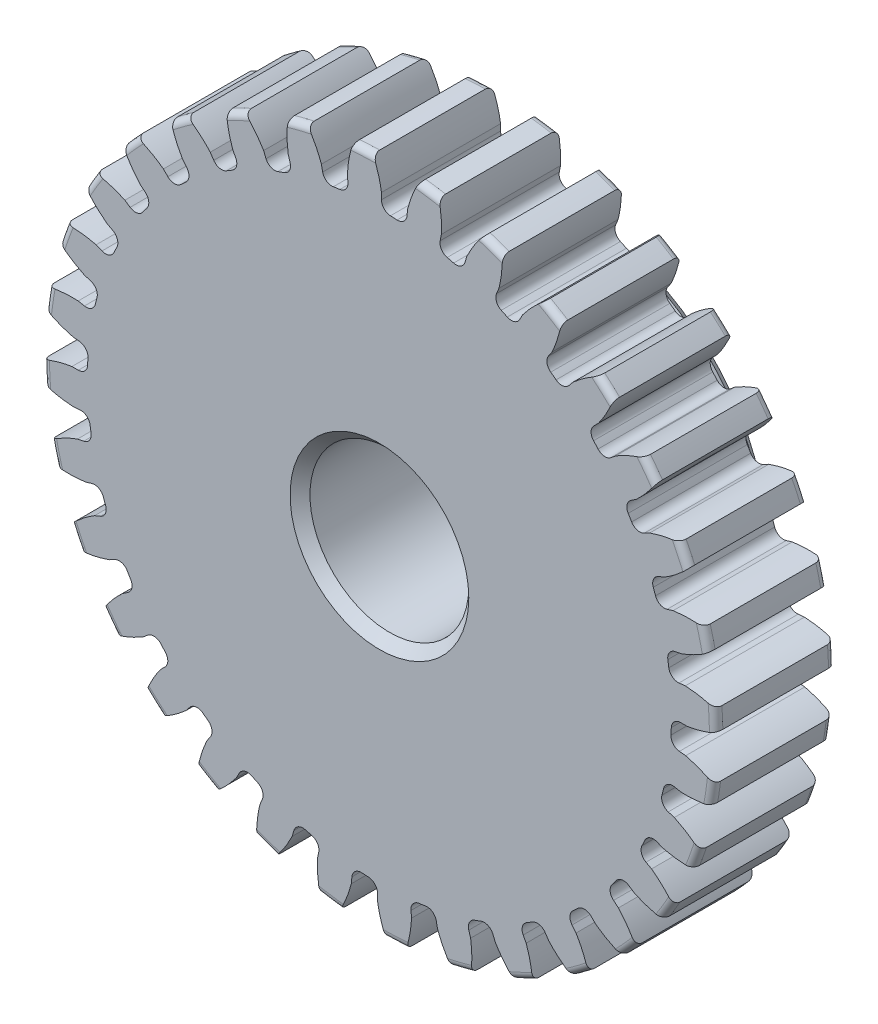
SolidWorks part; units mm, degrees
ref_plane "Front" through (0, 0, 0) normal (0, 0, 1) x (1, 0, 0)
ref_plane "Top" through (0, 0, 0) normal (0, 1, 0) x (1, 0, 0)
ref_plane "Right" through (0, 0, 0) normal (1, 0, 0) x (0, 0, -1)
sketch "Sketch1" plane through (0, 0, 0) normal (0, 0, 1) x (1, 0, 0)
  line L0 (-406.4, 0) -> (406.4, 0) construction
  circle A0 centre (0, 0) radius 13.462
  circle A1 centre (0, 0) radius 12.7 construction
  circle A3 centre (0, 0) radius 11.6761 construction
  dimension "D1" = 1.7859
  dimension "OD" = 26.924
  dimension "Ptich Dia" = 25.4
  dimension "Root Dia" = 23.3521
  dimension "D3" = 0.762
  dimension "Number of Teeth" = 812.8
extrude "Boss-Extrude1" add sketch "Sketch1" against normal blind 4.7625
sketch "Sketch2" plane through (0, 0, 0) normal (1, 0, 0) x (0, 0, -1)
  line L0 (4.7625, 0) -> (7.9375, 0)
  line L1 (4.7625, 0) -> (4.7625, 7.9375)
  line L2 (4.7625, 7.9375) -> (7.9375, 7.9375)
  line L3 (7.9375, 7.9375) -> (7.9375, 0)
  point P5 (7.9375, -7.9375)
  point P6 (0, -13.462)
  point P7 (4.7625, -13.462)
  point P9 (0, 13.462)
  dimension "Face Wd" = 4.7625
  dimension "B Hub Dia" = 15.875
  dimension "D O'all Lg." = 7.9375
revolve "Revolve1" add sketch "Sketch2" angle 360 about L0
fillet "Fillet2" radius 0.2692 3 edges at (13.462, 0, -4.7625) (13.462, 0, 0) (7.9375, 0, -4.7625)
sketch "Sketch3" plane through (0, 0, 0) normal (0, 0, 1) x (1, 0, 0)
  line L0 (0, 0) -> (0, 13.462) construction
  line L1 (-3.0785, 11.9038) -> (0, 12.7)
  line L2 (-9.5921, 12.7) -> (9.5921, 12.7) construction
  line L3 (-9.2865, 10.2983) -> (9.2865, 15.1017) construction
  line L4 (-3.0785, 11.9038) -> (0, 0) construction
  line L5 (-7.8523, 9.4615) -> (0, 0) construction
  line L6 (-7.8523, 9.4615) -> (-1.2652, 14.9283) construction
  line L7 (-2.1466, 12.1066) -> (0, 0) construction
  line L8 (-2.1466, 12.1066) -> (0.045, 12.4952) construction
  arc A0 (-3.0785, 11.9038) -> (-7.8523, 9.4615) centre (0, 0) ccw
  circle A1 centre (0, 0) radius 12.7 construction
  circle A2 centre (0, 0) radius 12.2955 construction
  arc A3 (-3.0785, 11.9038) -> (-2.1466, 12.1066) centre (0, 0) cw
  circle A4 centre (0, 0) radius 13.462 construction
  point P6 (0, 12.7)
  dimension "D1" = 3.1798
  dimension "Pressure Angle" = 14.5
  dimension "D2" = 5.4057
  dimension "D3" = 8.5601
  dimension "D4" = 0.9539
  dimension "D5" = 2.2259
sketch "Sketch4" plane through (0, 0, 0) normal (0, 0, 1) x (1, 0, 0)
  line L0 (0, 0) -> (0.6224, 12.6694) construction
  line L1 (0.0798, 12.2952) -> (0.0798, 11.6758)
  line L2 (0, 12.7) -> (1.2448, 12.6388) construction
  line L3 (1.1257, 12.2438) -> (1.065, 11.6274)
  line L4 (0.0798, 11.6758) -> (0, 0) construction
  line L5 (0, 0) -> (0, 13.462) construction
  line L6 (-7.8523, 9.4615) -> (-1.2652, 14.9283) construction
  line L7 (-7.8523, 9.4615) -> (-1.2652, 14.9283) construction
  arc A0 (1.065, 11.6274) -> (0.0798, 11.6758) centre (0, 0) ccw
  arc A1 (0, 12.7) -> (1.2448, 12.6388) centre (0, 0) cw construction
  circle A2 centre (0, 0) radius 12.7 construction
  circle A3 centre (0, 0) radius 12.2955 construction
  circle A4 centre (0, 0) radius 11.6761 construction
  arc A5 (2.7223, 14.7324) -> (-1.2652, 14.9283) centre (0, 0) ccw
  spline S0 degree 2 poles (-1.2652, 14.9283) (-0.1435, 13.7672) (0.0798, 12.2952) knots 0 0 0 1 1 1
  spline S1 degree 2 poles (2.7223, 14.7324) (1.4922, 13.6868) (1.1257, 12.2438) knots 0 0 0 1 1 1
  dimension "D1" = 1.2468
extrude "Cut-Extrude1" cut sketch "Sketch4" against normal through all
fillet "Fillet1" radius 0.374 2 edges at (1.065, 11.6274, -2.3813) (0.0798, 11.6758, -2.3813)
pattern_circular "CirPattern1" count 32 over 360 about axis through (0, 0, -4.7625) along (0, 0, 1) of "Cut-Extrude1", "Fillet1"
sketch "Sketch5" plane through (0, 0, 0) normal (0, 0, 1) x (1, 0, 0)
  circle A0 centre (0, 0) radius 3.175
  circle A1 centre (0, 0) radius 1.5875 construction
  dimension "Bore Min" = 6.35
  dimension "Bore Max" = 3.175
extrude "Cut-Extrude2" cut sketch "Sketch5" against normal through all
chamfer "Chamfer1" distance 0.3969 angle 45 3 edges at (7.9375, 0, -7.9375) (3.175, 0, 0) (3.175, 0, -7.9375)
sketch "Pitch Dia" plane through (0, 0, 0) normal (0, 0, 1) x (1, 0, 0)
  circle A0 centre (0, 0) radius 12.7 construction
  circle A1 centre (0, 0) radius 12.7 construction
equation "\"D1@Boss-Extrude1\" = \"Face Wd@Sketch2\""
equation "\"D2@Sketch3\" = \"D1@Sketch3\"*1.7"
equation "\"D3@Sketch3\" = \"D1@Sketch3\"+\"D2@Sketch3\"-.001"
equation "\"D4@Sketch3\" = \"D1@Sketch3\"*.3"
equation "\"D5@Sketch3\" = \"D1@Sketch3\"-\"D4@Sketch3\""
equation "\"D1@Sketch4\" = 1.5708/(\"Number of Teeth@Sketch1\"/\"Ptich Dia@Sketch1\")"
equation "\"D1@Chamfer1\" = \"B Hub Dia@Sketch2\"*.025"
equation "\"D1@CirPattern1\" = \"Number of Teeth@Sketch1\""
equation "\"D1@Fillet1\" = \"D1@Sketch4\"*.3"
equation "\"D1@Fillet2\" = \"OD@Sketch1\"*.01"
equation "\"D1@Sketch1\" = 2.250/(\"Number of Teeth@Sketch1\"/\"Ptich Dia@Sketch1\")"
